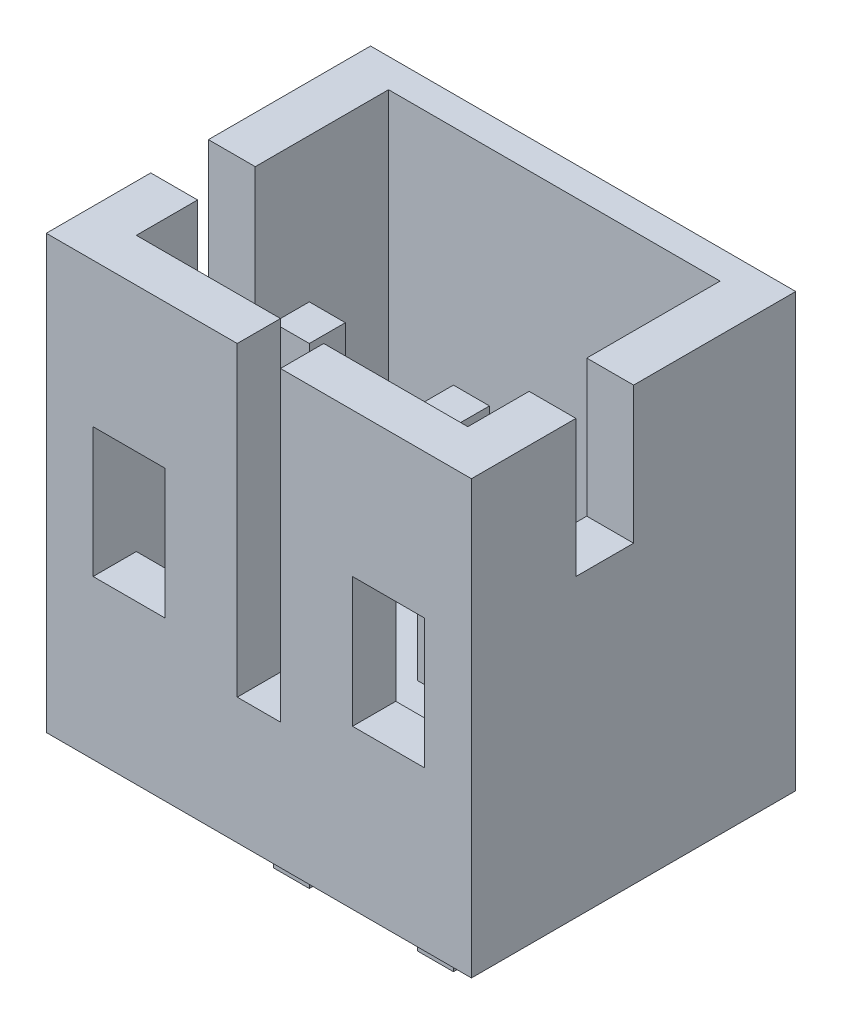
SolidWorks part; units mm, degrees
ref_plane "Front Plane" through (0, 0, 0) normal (0, 0, 1) x (1, 0, 0)
ref_plane "Top Plane" through (0, 0, 0) normal (0, 1, 0) x (1, 0, 0)
ref_plane "Right Plane" through (0, 0, 0) normal (1, 0, 0) x (0, 0, -1)
ref_plane "Plane1" through (4.6, 0, 0) normal (-1, 0, 0) x (0, -1, 0)
sketch "Sketch1" plane through (4.6, 0, 0) normal (-1, 0, 0) x (0, -1, 0)
  line L0 (0, 4.5) -> (-1.75, 4.5)
  line L1 (-1.75, 4.5) -> (-1.75, 0.4)
  line L2 (-1.75, 0.4) -> (0, 0.4)
  line L3 (0, 0.4) -> (0, 4.5)
extrude "Boss-Extrude1" add sketch "Sketch1" against normal blind 1.6
sketch "Sketch2" plane through (6.2, 0, 0) normal (1, 0, 0) x (0, 0, -1)
  line L0 (-3.9, 1.75) -> (-0.4, 1.75)
  line L1 (-0.4, 1.75) -> (-0.4, 0)
  line L2 (-0.4, 0) -> (-4.5, 0)
  line L3 (-4.5, 0) -> (-4.5, 2.2)
  line L4 (-4.5, 2.2) -> (-3.9, 2.2)
  line L5 (-3.9, 2.2) -> (-3.9, 1.75)
extrude "Boss-Extrude2" add sketch "Sketch2" along normal blind 2
sketch "Sketch3" plane through (0, 2.2, 0) normal (0, 1, 0) x (-1, 0, 0)
  line L0 (-6.2, 3.9) -> (-7.2, 3.9)
  line L1 (-7.2, 3.9) -> (-7.2, 4.5)
  line L2 (-7.2, 4.5) -> (-6.2, 4.5)
  line L3 (-6.2, 4.5) -> (-6.2, 3.9)
extrude "Boss-Extrude3" add sketch "Sketch3" along normal blind 1.8
sketch "Sketch4" plane through (0, 1.75, 0) normal (0, 1, 0) x (-1, 0, 0)
  line L0 (-5.6, 4.5) -> (-4.6, 4.5)
  line L1 (-4.6, 4.5) -> (-4.6, 3.9)
  line L2 (-4.6, 3.9) -> (-5.6, 3.9)
  line L3 (-5.6, 3.9) -> (-5.6, 4.5)
extrude "Boss-Extrude4" add sketch "Sketch4" along normal blind 2.25
sketch "Sketch5" plane through (4.6, 0, 0) normal (-1, 0, 0) x (0, 0, 1)
  line L0 (0.4, 0) -> (0.4, 1.75)
  line L1 (0.4, 1.75) -> (3.9, 1.75)
  line L2 (3.9, 1.75) -> (3.9, 2.2)
  line L3 (3.9, 2.2) -> (4.5, 2.2)
  line L4 (4.5, 2.2) -> (4.5, 0)
  line L5 (4.5, 0) -> (0.4, 0)
extrude "Boss-Extrude5" add sketch "Sketch5" along normal blind 1
sketch "Sketch6" plane through (3.6, 0, 0) normal (-1, 0, 0) x (0, 0, 1)
  line L0 (4.5, 4) -> (4.5, 0)
  line L1 (4.5, 0) -> (0.4, 0)
  line L2 (0.4, 0) -> (0.4, 4)
  line L3 (0.4, 4) -> (4.5, 4)
extrude "Boss-Extrude6" add sketch "Sketch6" along normal blind 0.65
sketch "Sketch7" plane through (0, 4, 0) normal (0, 1, 0) x (-1, 0, 0)
  line L0 (-8.2, 3.9) -> (-8.2, 4.5)
  line L1 (-8.2, 4.5) -> (-6.2, 4.5)
  line L2 (-6.2, 4.5) -> (-6.2, 3.9)
  line L3 (-6.2, 3.9) -> (-8.2, 3.9)
  line L4 (-3.6, 0.4) -> (-3.6, 3.9)
  line L5 (-3.6, 3.9) -> (-5.6, 3.9)
  line L6 (-5.6, 3.9) -> (-5.6, 4.5)
  line L7 (-5.6, 4.5) -> (-2.95, 4.5)
  line L8 (-2.95, 4.5) -> (-2.95, 0.4)
  line L9 (-2.95, 0.4) -> (-3.6, 0.4)
extrude "Boss-Extrude7" add sketch "Sketch7" along normal blind 2
sketch "Sketch8" plane through (8.2, 0, 0) normal (1, 0, 0) x (0, 0, -1)
  line L0 (-0.4, 6) -> (-0.4, 0)
  line L1 (-0.4, 0) -> (-4.5, 0)
  line L2 (-4.5, 0) -> (-4.5, 6)
  line L3 (-4.5, 6) -> (-0.4, 6)
extrude "Boss-Extrude8" add sketch "Sketch8" along normal blind 0.65
sketch "Sketch9" plane through (0, 0, 0.4) normal (0, 0, -1) x (-1, 0, 0)
  line L0 (-2.95, 0) -> (-8.85, 0)
  line L1 (-8.85, 0) -> (-8.85, 6)
  line L2 (-8.85, 6) -> (-2.95, 6)
  line L3 (-2.95, 6) -> (-2.95, 0)
extrude "Boss-Extrude9" add sketch "Sketch9" along normal blind 0.4
sketch "Sketch10" plane through (3.6, 0, 0) normal (1, 0, 0) x (0, 0, -1)
  line L0 (-2.25, 6) -> (-3.05, 6)
  line L1 (-3.05, 6) -> (-3.05, 4.1)
  line L2 (-3.05, 4.1) -> (-2.25, 4.1)
  line L3 (-2.25, 4.1) -> (-2.25, 6)
extrude "Cut-Extrude1" cut sketch "Sketch10" against normal through all
sketch "Sketch11" plane through (8.85, 0, 0) normal (1, 0, 0) x (0, 0, -1)
  line L0 (-3.05, 6) -> (-3.05, 4.1)
  line L1 (-3.05, 4.1) -> (-2.25, 4.1)
  line L2 (-2.25, 4.1) -> (-2.25, 6)
  line L3 (-2.25, 6) -> (-3.05, 6)
extrude "Cut-Extrude2" cut sketch "Sketch11" against normal through all
sketch "Sketch12" plane through (0, 1.75, 0) normal (0, 1, 0) x (-1, 0, 0)
  line L0 (-4.65, 2.55) -> (-5.15, 2.55)
  line L1 (-5.15, 2.55) -> (-5.15, 3.05)
  line L2 (-5.15, 3.05) -> (-4.65, 3.05)
  line L3 (-4.65, 3.05) -> (-4.65, 2.55)
extrude "Boss-Extrude10" add sketch "Sketch12" along normal blind 3.3
sketch "Sketch13" plane through (0, 1.75, 0) normal (0, 1, 0) x (-1, 0, 0)
  line L0 (-6.65, 2.55) -> (-7.15, 2.55)
  line L1 (-7.15, 2.55) -> (-7.15, 3.05)
  line L2 (-7.15, 3.05) -> (-6.65, 3.05)
  line L3 (-6.65, 3.05) -> (-6.65, 2.55)
extrude "Boss-Extrude11" add sketch "Sketch13" along normal blind 3.3
sketch "Sketch14" plane through (0, 0, 0) normal (0, -1, 0) x (1, 0, 0)
  line L0 (5.15, 3.05) -> (5.15, 2.55)
  line L1 (5.15, 2.55) -> (4.65, 2.55)
  line L2 (4.65, 2.55) -> (4.65, 3.05)
  line L3 (4.65, 3.05) -> (5.15, 3.05)
extrude "Boss-Extrude12" add sketch "Sketch14" along normal blind 1.5
sketch "Sketch15" plane through (0, 0, 0) normal (0, -1, 0) x (1, 0, 0)
  line L0 (7.15, 3.05) -> (7.15, 2.55)
  line L1 (7.15, 2.55) -> (6.65, 2.55)
  line L2 (6.65, 2.55) -> (6.65, 3.05)
  line L3 (6.65, 3.05) -> (7.15, 3.05)
extrude "Boss-Extrude13" add sketch "Sketch15" along normal blind 1.5
